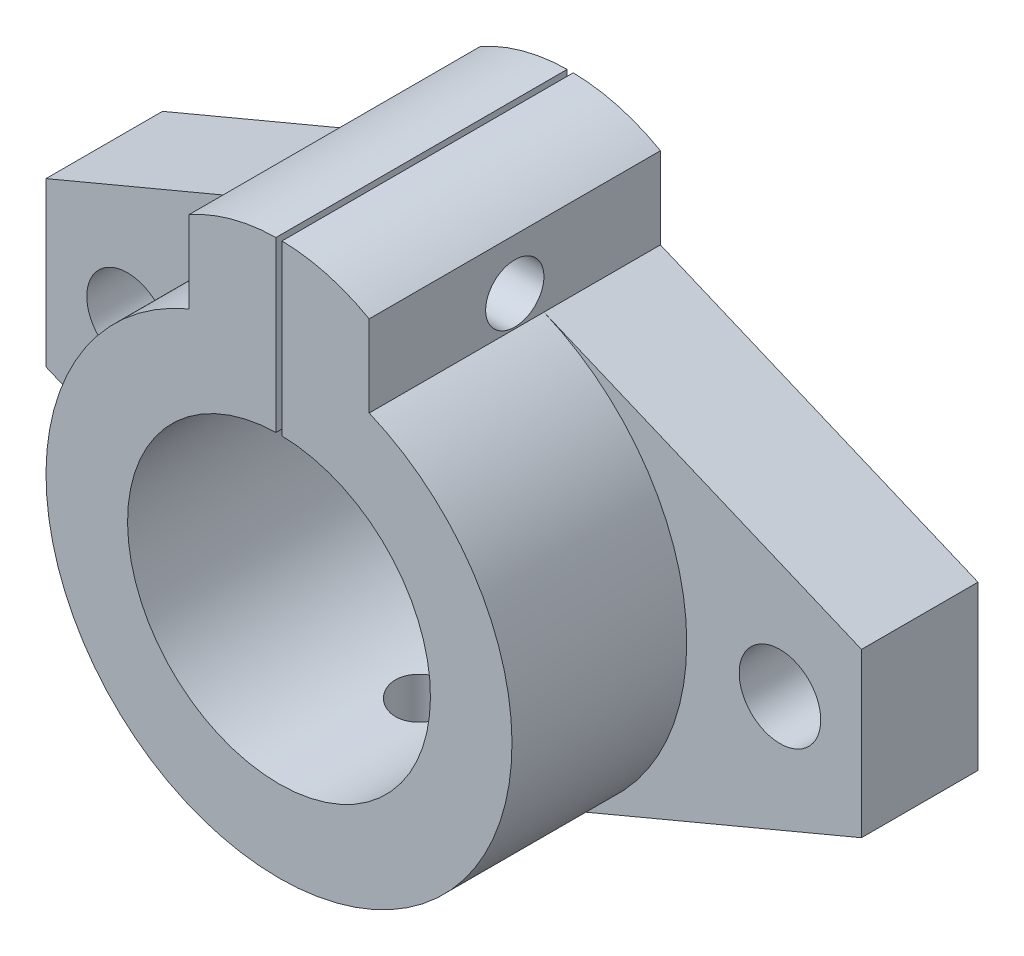
SolidWorks part; units mm, degrees
material "6061 合金"
ref_plane "前视基准面" through (0, 0, 0) normal (0, 0, 1) x (1, 0, 0)
ref_plane "上视基准面" through (0, 0, 0) normal (0, 1, 0) x (1, 0, 0)
ref_plane "右视基准面" through (0, 0, 0) normal (1, 0, 0) x (0, 0, -1)
sketch "草图1" plane through (0, 0, 0) normal (0, 0, 1) x (1, 0, 0)
  line L0 (-7.7403, 18.4415) -> (-7.7403, 25.4415)
  line L1 (-35, -7) -> (-35, 7)
  line L2 (-35, 7) -> (-7.7403, 18.4415)
  line L3 (-35, -7) -> (-7.7403, -18.4415)
  line L4 (7.7403, 18.4415) -> (7.7403, 25.4415)
  line L5 (35, -7) -> (7.7403, -18.4415)
  line L6 (35, -7) -> (35, 7)
  line L7 (35, 7) -> (7.7403, 18.4415)
  line L8 (0, 0) -> (-28, 0) construction
  circle A0 centre (0, 0) radius 13
  arc A1 (-7.7403, 18.4415) -> (7.7403, 18.4415) centre (0, 0) ccw
  arc A2 (-7.7403, 25.4415) -> (7.7403, 25.4415) centre (0, 11.8749) cw
  circle A3 centre (-28, 0) radius 3.5
  circle A4 centre (28, 0) radius 3.5
  dimension "D1" = 28
  dimension "D3" = 26
  dimension "D4" = 20
  dimension "D5" = 7
  dimension "D6" = 7
  dimension "D2" = 28
  dimension "D7" = 70
extrude "凸台-拉伸2" add sketch "草图1" along normal blind 10 contours A1 L5 L6 L7 | A2 L0 A1 L4 A0 | A1 L2 L1 L3
sketch "草图2" plane through (0, 0, 10) normal (0, 0, 1) x (1, 0, 0)
  line L0 (-7.7403, 18.4415) -> (-7.7403, 25.4415)
  line L1 (7.7403, 18.4415) -> (7.7403, 25.4415)
  circle A0 centre (0, 0) radius 13
  arc A1 (-7.7403, 18.4415) -> (7.7403, 18.4415) centre (0, 0) ccw
  arc A2 (-7.7403, 25.4415) -> (7.7403, 25.4415) centre (0, 11.8749) cw
extrude "凸台-拉伸3" add sketch "草图2" along normal blind 15
sketch "草图3" plane through (0, 0, 25) normal (0, 0, 1) x (1, 0, 0)
  line L1 (-0.2586, 12.3781) -> (-0.2586, 31.1043)
  line L2 (0.2586, 12.3781) -> (0.2586, 31.1043)
  line L3 (-0.2586, 12.3781) -> (0.2586, 12.3781)
  line L4 (-0.2586, 31.1043) -> (0.2586, 31.1043)
extrude "切除-拉伸1" cut sketch "草图3" against normal through all
sketch "草图4" plane through (7.7403, 0, 0) normal (1, 0, 0) x (0, 0, -1)
  circle A0 centre (-12.5, 21.0864) radius 2.5
extrude "切除-拉伸2" cut sketch "草图4" against normal through all
sketch "草图5" plane through (0, 0, 0) normal (0, 1, 0) x (1, 0, 0)
  line L0 (0, 0) -> (0, -25) construction
  line L1 (7.7403, 0) -> (-7.7403, 0) construction
  line L2 (-20, -25) -> (20, -25) construction
  circle A0 centre (0, -12.5) radius 2.5
  dimension "D1" = 5
  dimension "D2" = 12.5
extrude "切除-拉伸3" cut sketch "草图5" against normal through all
